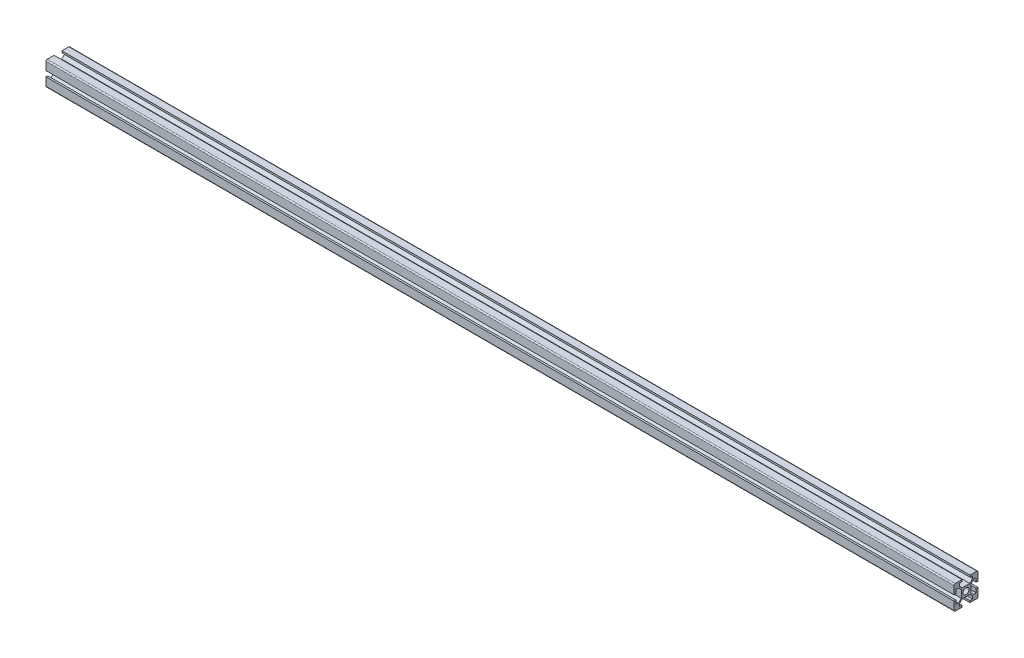
SolidWorks part; units mm, degrees
ref_plane "前视基准面" through (0, 0, 0) normal (0, 0, 1) x (1, 0, 0)
ref_plane "上视基准面" through (0, 0, 0) normal (0, 1, 0) x (1, 0, 0)
ref_plane "右视基准面" through (0, 0, 0) normal (1, 0, 0) x (0, 0, -1)
sketch "草图1" plane through (0, 0, 0) normal (0, 0, 1) x (1, 0, 0)
  line L0 (0, 0) -> (760, 0)
other "铝型材 20 X 20 X 2(1)"
ref_plane "基准面6" through (0, 0, 0) normal (1, 0, 0) x (0, 1, 0)
sketch "草图11" plane through (0, 0, 0) normal (1, 0, 0) x (0, 1, 0)
  line L175 (-10, 9) -> (-10, 3.25)
  line L176 (-9, -10) -> (-2.25, -10)
  line L177 (-10, -3.25) -> (-10, -9)
  line L178 (-9, 10) -> (-2.25, 10)
  line L179 (-2.25, -8.5) -> (-2.25, -10)
  line L180 (-2.25, 8.5) -> (-2.25, 10)
  line L181 (-8.5, 3.25) -> (-10, 3.25)
  line L182 (-8.5, 5.5) -> (-8.5, 3.25)
  line L183 (-10, 0) -> (10, 0) construction
  line L184 (-3.1515, -4) -> (3.1515, -4)
  line L185 (-3.1515, 4) -> (3.1515, 4)
  line L186 (-8.5, 5.5) -> (-6.3485, 5.5)
  line L187 (0, -10) -> (0, 10) construction
  line L188 (-4, -3.1515) -> (-4, 3.1515)
  line L189 (-8.5, -3.25) -> (-10, -3.25)
  line L190 (-8.5, -5.5) -> (-8.5, -3.25)
  line L191 (-8.5, -5.5) -> (-6.3485, -5.5)
  line L192 (-4, 3.1515) -> (-6.3485, 5.5)
  line L193 (-4, -3.1515) -> (-6.3485, -5.5)
  line L194 (-5.5, -8.5) -> (-2.25, -8.5)
  line L195 (-5.5, -8.5) -> (-5.5, -6.3485)
  line L196 (-3.1515, -4) -> (-5.5, -6.3485)
  line L197 (-5.5, 8.5) -> (-2.25, 8.5)
  line L198 (-5.5, 8.5) -> (-5.5, 6.3485)
  line L199 (-3.1515, 4) -> (-5.5, 6.3485)
  line L200 (10, 9) -> (10, 3.25)
  line L201 (9, -10) -> (2.25, -10)
  line L202 (10, -3.25) -> (10, -9)
  line L203 (9, 10) -> (2.25, 10)
  line L204 (2.25, -8.5) -> (2.25, -10)
  line L205 (2.25, 8.5) -> (2.25, 10)
  line L206 (8.5, 3.25) -> (10, 3.25)
  line L207 (8.5, 5.5) -> (8.5, 3.25)
  line L208 (8.5, 5.5) -> (6.3485, 5.5)
  line L209 (4, -3.1515) -> (4, 3.1515)
  line L210 (8.5, -3.25) -> (10, -3.25)
  line L211 (8.5, -5.5) -> (8.5, -3.25)
  line L212 (8.5, -5.5) -> (6.3485, -5.5)
  line L213 (4, 3.1515) -> (6.3485, 5.5)
  line L214 (4, -3.1515) -> (6.3485, -5.5)
  line L215 (5.5, -8.5) -> (2.25, -8.5)
  line L216 (5.5, -8.5) -> (5.5, -6.3485)
  line L217 (3.1515, -4) -> (5.5, -6.3485)
  line L218 (5.5, 8.5) -> (2.25, 8.5)
  line L219 (5.5, 8.5) -> (5.5, 6.3485)
  line L220 (3.1515, 4) -> (5.5, 6.3485)
  arc A28 (-10, -9) -> (-9, -10) centre (-9, -9) ccw
  arc A29 (-9, 10) -> (-10, 9) centre (-9, 9) ccw
  circle A30 centre (0, 0) radius 2.5
  arc A31 (9, -10) -> (10, -9) centre (9, -9) ccw
  arc A32 (10, 9) -> (9, 10) centre (9, 9) ccw
  point P0 (0, 0)
